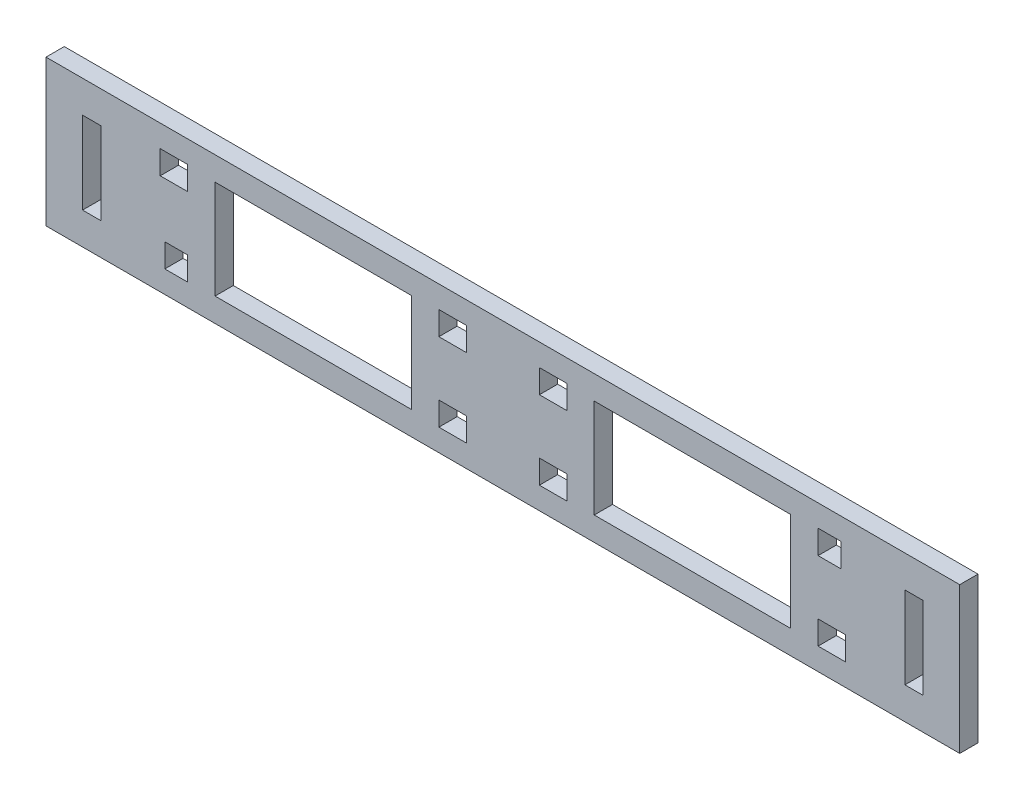
SolidWorks part; units mm, degrees
ref_plane "Front Plane" through (0, 0, 0) normal (0, 0, 1) x (1, 0, 0)
ref_plane "Top Plane" through (0, 0, 0) normal (0, 1, 0) x (1, 0, 0)
ref_plane "Right Plane" through (0, 0, 0) normal (1, 0, 0) x (0, 0, -1)
sketch "Sketch2" plane through (0, 0, 0) normal (0, 0, 1) x (1, 0, 0)
  line L1 (-79.3343, 40.1154) -> (120.6657, 40.1154)
  line L2 (-79.3343, 40.1154) -> (-79.3343, 8.1154)
  line L3 (-79.3343, 8.1154) -> (120.6657, 8.1154)
  line L4 (120.6657, 40.1154) -> (120.6657, 8.1154)
  dimension "D1" = 200
  dimension "D2" = 32
extrude "Boss-Extrude1" add sketch "Sketch2" along normal blind 4
sketch "Sketch3" plane through (0, 0, 4) normal (0, 0, 1) x (1, 0, 0)
  line L1 (-42.3343, 34.9154) -> (0.6657, 34.9154)
  line L2 (-42.3343, 34.9154) -> (-42.3343, 13.3154)
  line L3 (-42.3343, 13.3154) -> (0.6657, 13.3154)
  line L4 (0.6657, 34.9154) -> (0.6657, 13.3154)
  line L5 (40.6657, 34.9154) -> (83.6657, 34.9154)
  line L6 (40.6657, 34.9154) -> (40.6657, 13.3154)
  line L7 (40.6657, 13.3154) -> (83.6657, 13.3154)
  line L8 (83.6657, 34.9154) -> (83.6657, 13.3154)
  line L10 (-18.3343, 24.1154) -> (-39.8343, 24.1154)
  line L11 (28.6657, 35.2654) -> (34.6657, 35.2654)
  line L12 (28.6657, 35.2654) -> (28.6657, 30.1154)
  line L13 (-54.3343, 35.2654) -> (-48.3343, 35.2654)
  line L14 (-54.3343, 35.2654) -> (-54.3343, 30.1154)
  line L15 (-54.3343, 30.1154) -> (-48.3343, 30.1154)
  line L16 (-48.3343, 35.2654) -> (-48.3343, 30.1154)
  line L17 (-53.3343, 18.1154) -> (-48.3343, 18.1154)
  line L18 (-53.3343, 18.1154) -> (-53.3343, 12.9654)
  line L19 (-53.3343, 12.9654) -> (-48.3343, 12.9654)
  line L20 (-48.3343, 18.1154) -> (-48.3343, 12.9654)
  line L21 (6.6657, 35.2654) -> (12.6657, 35.2654)
  line L22 (6.6657, 35.2654) -> (6.6657, 30.1154)
  line L23 (6.6657, 30.1154) -> (12.6657, 30.1154)
  line L24 (12.6657, 35.2654) -> (12.6657, 30.1154)
  line L25 (6.6657, 18.1154) -> (12.6657, 18.1154)
  line L26 (6.6657, 18.1154) -> (6.6657, 12.9654)
  line L27 (6.6657, 12.9654) -> (12.6657, 12.9654)
  line L28 (12.6657, 18.1154) -> (12.6657, 12.9654)
  line L29 (28.6657, 30.1154) -> (34.6657, 30.1154)
  line L30 (34.6657, 35.2654) -> (34.6657, 30.1154)
  line L31 (-71.3343, 33.1154) -> (-67.3343, 33.1154)
  line L32 (-71.3343, 33.1154) -> (-71.3343, 15.1154)
  line L33 (28.6657, 18.1154) -> (34.6657, 18.1154)
  line L34 (28.6657, 18.1154) -> (28.6657, 12.9654)
  line L35 (28.6657, 12.9654) -> (34.6657, 12.9654)
  line L36 (34.6657, 18.1154) -> (34.6657, 12.9654)
  line L37 (89.6657, 35.3154) -> (94.6657, 35.3154)
  line L38 (89.6657, 35.3154) -> (89.6657, 30.1154)
  line L39 (89.6657, 30.1154) -> (94.6657, 30.1154)
  line L40 (94.6657, 35.3154) -> (94.6657, 30.1154)
  line L41 (89.6657, 18.1154) -> (95.6657, 18.1154)
  line L42 (89.6657, 18.1154) -> (89.6657, 12.9654)
  line L43 (89.6657, 12.9654) -> (95.6657, 12.9654)
  line L44 (95.6657, 18.1154) -> (95.6657, 12.9654)
  line L45 (-71.3343, 15.1154) -> (-67.3343, 15.1154)
  line L46 (-67.3343, 33.1154) -> (-67.3343, 15.1154)
  line L48 (108.6657, 33.1154) -> (112.6657, 33.1154)
  line L49 (108.6657, 33.1154) -> (108.6657, 15.1154)
  line L50 (108.6657, 15.1154) -> (112.6657, 15.1154)
  line L51 (112.6657, 33.1154) -> (112.6657, 15.1154)
  dimension "D2" = 43
  dimension "D3" = 21.6
  dimension "D5" = 10.8
  dimension "D6" = 5.15
  dimension "D7" = 21.6
  dimension "D8" = 43
  dimension "D9" = 6
  dimension "D10" = 6
  dimension "D11" = 6
  dimension "D12" = 6
  dimension "D13" = 6
  dimension "D14" = 6
  dimension "D15" = 6
  dimension "D16" = 6
  dimension "D17" = 6
  dimension "D18" = 6
  dimension "D19" = 6
  dimension "D20" = 6
  dimension "D21" = 6
  dimension "D22" = 6
  dimension "D23" = 6
  dimension "D24" = 6
  dimension "D25" = 6
  dimension "D26" = 6
  dimension "D27" = 5.15
  dimension "D28" = 5.15
  dimension "D29" = 6
  dimension "D30" = 5.15
  dimension "D31" = 5.15
  dimension "D32" = 6
  dimension "D33" = 5.15
  dimension "D34" = 6
  dimension "D35" = 40
  dimension "D36" = 5.15
  dimension "D37" = 25
  dimension "D41" = 4
  dimension "D43" = 25
extrude "Cut-Extrude1" cut sketch "Sketch3" against normal blind 4
